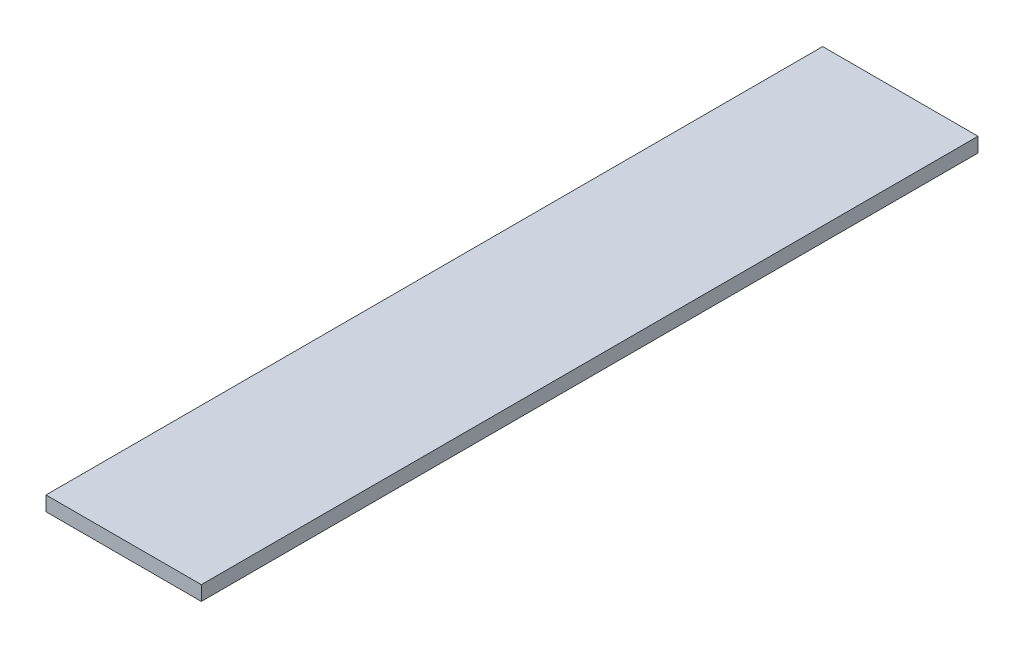
SolidWorks part; units mm, degrees
ref_plane "Front Plane" through (0, 0, 0) normal (0, 0, 1) x (1, 0, 0)
ref_plane "Top Plane" through (0, 0, 0) normal (0, 1, 0) x (1, 0, 0)
ref_plane "Right Plane" through (0, 0, 0) normal (1, 0, 0) x (0, 0, -1)
sketch "Sketch1" plane through (0, 0, 0) normal (0, 1, 0) x (1, 0, 0)
  line L1 (0, 0) -> (50.8, 0)
  line L2 (0, 0) -> (0, -254)
  line L3 (0, -254) -> (50.8, -254)
  line L4 (50.8, 0) -> (50.8, -254)
  dimension "D1" = 254
  dimension "D2" = 50.8
extrude "Boss-Extrude1" add sketch "Sketch1" along normal blind 4.7625 contours L1 L4 L3 L2
ref_plane "Plane1" through (50.8, 4.7625, 254) normal (1, 0, 0) x (0, 0, -1)
ref_plane "Plane2" through (0, 0, 254) normal (1, 0, 0) x (0, 0, -1)
